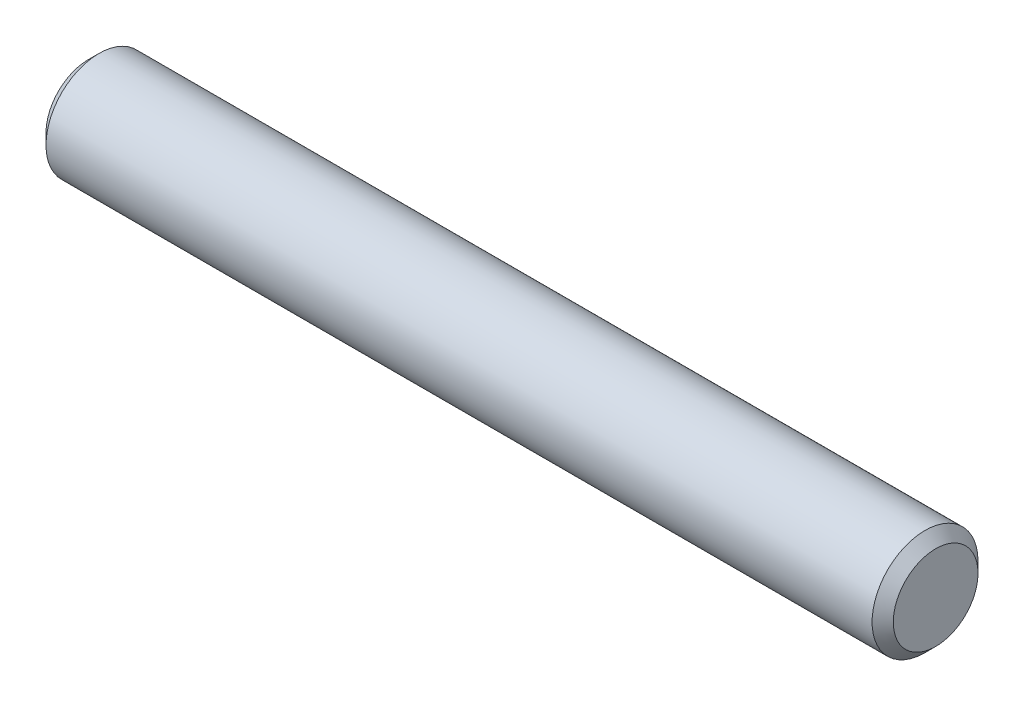
SolidWorks part; units mm, degrees
ref_plane "Front" through (0, 0, 0) normal (0, 0, 1) x (1, 0, 0)
ref_plane "Top" through (0, 0, 0) normal (0, 1, 0) x (1, 0, 0)
ref_plane "Right" through (0, 0, 0) normal (1, 0, 0) x (0, 0, -1)
sketch "Sketch1" plane through (0, 0, 0) normal (0, 0, 1) x (1, 0, 0)
  line L0 (-25.4, 0) -> (25.4, 0) construction
  line L1 (25.4, 3.175) -> (25.4, -3.175) construction
  line L2 (-25.4, 3.175) -> (-25.4, -3.175) construction
  dimension "Length" = 50.8
  dimension "Diameter" = 6.35
sketch "Sketch2" plane through (0, 0, 0) normal (1, 0, 0) x (0, 0, -1)
  circle A0 centre (0, 0) radius 3.175
extrude "Extrude1" add sketch "Sketch2" against normal up to vertex (25.4 mm away) and the other way up to vertex (25.4 mm away) up to point (-25.4, 3.175, 0) other way up to point (25.4, 3.175, 0)
chamfer "Chamfer1" distance 0.635 angle 45 2 edges at (25.4, 0, -3.175) (-25.4, 0, -3.175)
equation "\"D1@Chamfer1\" = \"Diameter@Sketch1\"*.1"
